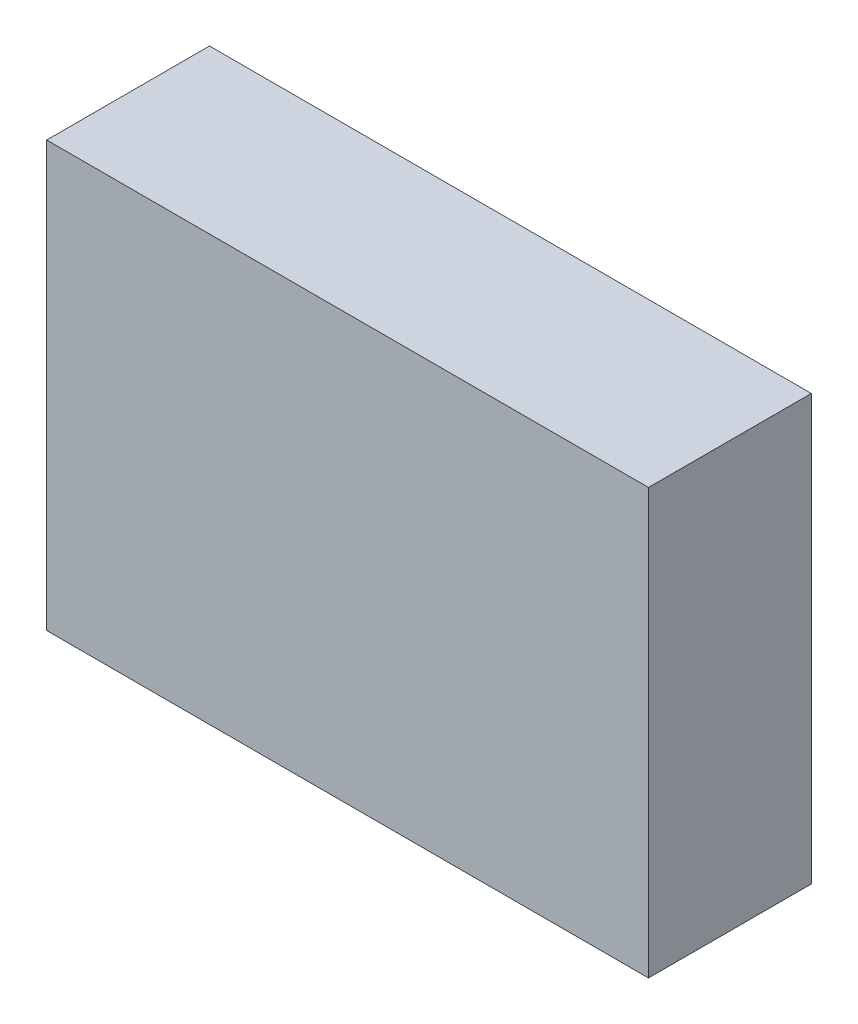
SolidWorks part; units mm, degrees
ref_plane "前视基准面" through (0, 0, 0) normal (0, 0, 1) x (1, 0, 0)
ref_plane "上视基准面" through (0, 0, 0) normal (0, 1, 0) x (1, 0, 0)
ref_plane "右视基准面" through (0, 0, 0) normal (1, 0, 0) x (0, 0, -1)
sketch "草图1" plane through (0, 0, 0) normal (0, 0, 1) x (1, 0, 0)
  line L0 (14.8362, 12.3126) -> (25.2381, 12.3126) construction
  line L1 (15.9996, 9.3126) -> (24.4996, 9.3126)
  line L2 (15.9996, 15.3126) -> (24.4996, 15.3126)
  line L3 (20.2496, 15.7334) -> (20.2496, 8.5637) construction
  line L4 (15.9996, 15.3126) -> (15.9996, 9.3126)
  line L5 (24.4996, 15.3126) -> (24.4996, 9.3126)
extrude "凸台-拉伸1" add sketch "草图1" along normal blind 2.3
